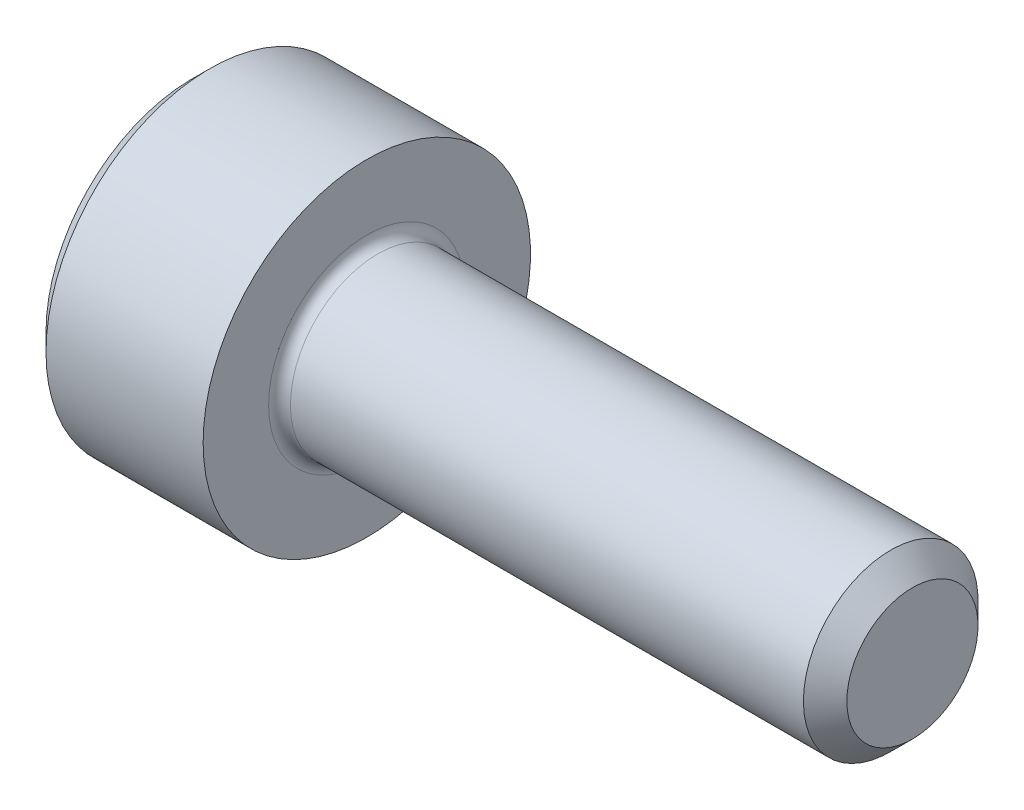
SolidWorks part; units mm, degrees
ref_plane "Plane1" through (0, 0, 0) normal (0, 0, 1) x (1, 0, 0)
ref_plane "Plane2" through (0, 0, 0) normal (0, 1, 0) x (1, 0, 0)
ref_plane "Plane3" through (0, 0, 0) normal (1, 0, 0) x (0, 0, -1)
sketch "BodySke" plane through (0, 0, 0) normal (0, 0, 1) x (1, 0, 0)
  line L0 (0, 0) -> (0, 1.34)
  line L1 (0.16, 1.5) -> (1.6, 1.5)
  line L2 (1.6, 1.5) -> (1.6, 0.8)
  line L3 (1.6, 0.8) -> (6.401, 0.8)
  line L4 (6.6, 0.601) -> (6.6, 0)
  line L5 (6.6, 0) -> (0, 0)
  line L6 (-31.75, 0) -> (127, 0) construction
  line L7 (0, 1.34) -> (0.16, 1.5)
  line L8 (6.6, 0.601) -> (6.401, 0.8)
  line L9 (0, -1.34) -> (0.16, -1.5) construction
  line L10 (6.6, -0.601) -> (6.401, -0.8) construction
  line L11 (1.95, 9.525) -> (1.95, 3.175) construction
  line L12 (1.6, 9.525) -> (1.6, 3.175) construction
  line L13 (-43.4, 9.525) -> (-43.4, 3.175) construction
  dimension "Diameter" = 1.6
  dimension "Head_ht" = 1.6
  dimension "Length" = 5
  dimension "Body_ch_ang" = 45
  dimension "Head_dia" = 3
  dimension "Head_ch_ang" = 45
  dimension "Minor_dia" = 1.202
  dimension "Advance" = 0.35
  dimension "Thread_nom" = 5
  dimension "Thread_length" = 50
  dimension "Head_ch_ht" = 0.16
revolve "Base-Revolve" add sketch "BodySke"
cosmetic thread "ThreadCosmetic" [suppressed]
fillet "Fillet1" radius 0.1 1 edges at (1.6, 0, 0.8)
sketch "Sketch2" plane through (0, 0, 0) normal (0, 0, 1) x (1, 0, 0)
  line L0 (0, 0.7725) -> (0.7, 0.7725)
  line L1 (0.7, 0.7725) -> (1.146, 0)
  line L2 (-31.75, 0) -> (127, 0) construction
  line L3 (1.146, 0) -> (0, 0)
  line L4 (0, 0) -> (0, 0.7725)
  line L5 (0, 1.34) -> (0, -1.34) construction
  line L6 (0, 0) -> (47.625, 0) construction
  line L7 (1.6, -1.5) -> (1.6, 1.5) construction
  dimension "D1" = 0.7725
  dimension "D2" = 60
  dimension "Wall_thickness" = 0.9
revolve "Hex-PreBroach" cut sketch "Sketch2" angle 360 about L6
sketch "Sketch3" plane through (0, 0, 0) normal (-1, 0, 0) x (0, 0.5, 0.866)
  line L0 (0.446, 0.7725) -> (-0.446, 0.7725)
  line L1 (-0.446, 0.7725) -> (-0.892, 0)
  line L2 (0.446, 0.7725) -> (0.892, 0)
  line L3 (0.446, -0.7725) -> (0.892, 0)
  line L4 (0.446, -0.7725) -> (-0.446, -0.7725)
  line L5 (-0.446, -0.7725) -> (-0.892, 0)
  dimension "D1" = 0.7725
  dimension "D2" = 0.7725
  dimension "Hex_size" = 1.545
extrude "Hex" cut sketch "Sketch3" against normal blind 0.7
sketch "Sketch4" plane through (0, 0, 0) normal (-1, 0, 0) x (0, 0, 1)
  line L0 (0, 0) -> (0.9398, 0)
  line L1 (0, 0) -> (6.1484, 3.5498) construction
  line L2 (0, 0) -> (0.4699, 0.8139)
  line L3 (0.7832, 0.2175) -> (0.8962, 0.2828)
  line L4 (0.58, 0.5695) -> (0.693, 0.6348)
  arc A0 (0.7832, 0.2175) -> (0.58, 0.5695) centre (0, 0) ccw
  arc A1 (0.9398, 0) -> (0.8962, 0.2828) centre (0, 0) ccw
  arc A2 (0.4699, 0.8139) -> (0.693, 0.6348) centre (0, 0) cw
  dimension "D1" = 30
  dimension "Spline_n_dim" = 1.6256
  dimension "Spline_m_dim" = 1.8796
  dimension "D2" = 60
  dimension "D3" = 0.2032
  dimension "Spline_p_dim" = 0.4064
extrude "Spline" [suppressed] cut sketch "Sketch4" against normal blind 0.7
pattern_circular "CirPattern1" [suppressed] count 6 every 60
sketch "Sketch5" plane through (0, 0, 0) normal (0, 0, 1) x (1, 0, 0)
  line L0 (-31.75, 0) -> (127, 0) construction
  line L2 (0, 1.34) -> (0, -1.34) construction
  circle A0 centre (0.1, 0) radius 0.005
  dimension "Drilled_hole_dia" = 0.01
  dimension "Drilled_hole_loc" = 0.1
extrude "Hole" [suppressed] cut sketch "Sketch5" against normal through all and the other way through all
pattern_circular "Drilled-4" [suppressed] count 2 every 60
pattern_circular "Drilled-6" [suppressed] count 3 every 60
sketch "ThdSchSke" plane through (0, 0, 0) normal (0, 0, 1) x (1, 0, 0)
  line L0 (1.95, -0.601) -> (1.8107, -0.8)
  line L1 (1.95, -0.601) -> (2.0893, -0.8)
  line L2 (2.0893, -0.8) -> (2.0893, -1)
  line L3 (-3.175, 0) -> (5.1513, 0) construction
  line L5 (2.0893, -1) -> (1.8107, -1)
  line L6 (1.8107, -1) -> (1.8107, -0.8)
  line L7 (0, 1.34) -> (0, -1.34) construction
  dimension "Thread_minor" = 1.202
  dimension "Diameter" = 1.6
  dimension "Start" = 1.95
  dimension "SideAngle" = 55
  dimension "VeeAngle" = 70
  dimension "Overcut" = 2
revolve "ThreadSchematic" [suppressed] cut sketch "ThdSchSke" angle 360 about L3
pattern_linear "ThdSchPat" [suppressed]
equation "\"D2@Sketch3\" = \"Hex_size@Sketch3\" / 2"
equation "\"D1@Sketch3\" = \"Hex_size@Sketch3\" / 2"
equation "\"D1@Sketch2\" = \"Hex_size@Sketch3\" / 2"
equation "\"D3@Sketch4\" = \"Spline_p_dim@Sketch4\" / 2"
equation "\"Thread_minor@ThreadCosmetic\"  =  \"Minor_dia@BodySke\""
equation "\"D2@CirPattern1\" = 360 / \"Num_teeth@CirPattern1\""
equation "\"Wall_thickness@Sketch2\" = \"Head_ht@BodySke\" - \"Key_eng@Hex\""
equation "\"Thread_length@ThreadCosmetic\" = ((sgn( (\"Length@BodySke\" - \"Advance@BodySke\" ) - \"Thread_nom@BodySke\" )-1)*( (\"Length@BodySke\" - \"Advance@BodySke\" ) - \"Thread_nom@BodySke\" ))/-2+ \"Thread_nom@BodySke\""
equation "\"Thread_minor@ThdSchSke\" = \"Minor_dia@BodySke\""
equation "\"Diameter@ThdSchSke\" = \"Diameter@BodySke\""
equation "\"Overcut@ThdSchSke\" = \"Diameter@BodySke\" * 1.25"
equation "\"Start@ThdSchSke\" = \"Head_ht@BodySke\" + \"Length@BodySke\" - \"Thread_length@ThreadCosmetic\"  '---Non-countersunk---"
equation "\"Num_threads@ThdSchPat\" = int( \"Thread_length@ThreadCosmetic\" / \"Advance@BodySke\" + 0.999 )  + 1"
equation "\"Advance@ThdSchPat\" = \"Thread_length@ThreadCosmetic\" /  (\"Num_threads@ThdSchPat\" - 1) 'relax it"
equation "\"Num_threads@ThdSchPat\" = \"Num_threads@ThdSchPat\" - sgn( \"Num_threads@ThdSchPat\" - 1) '---chamfered tips only---"
